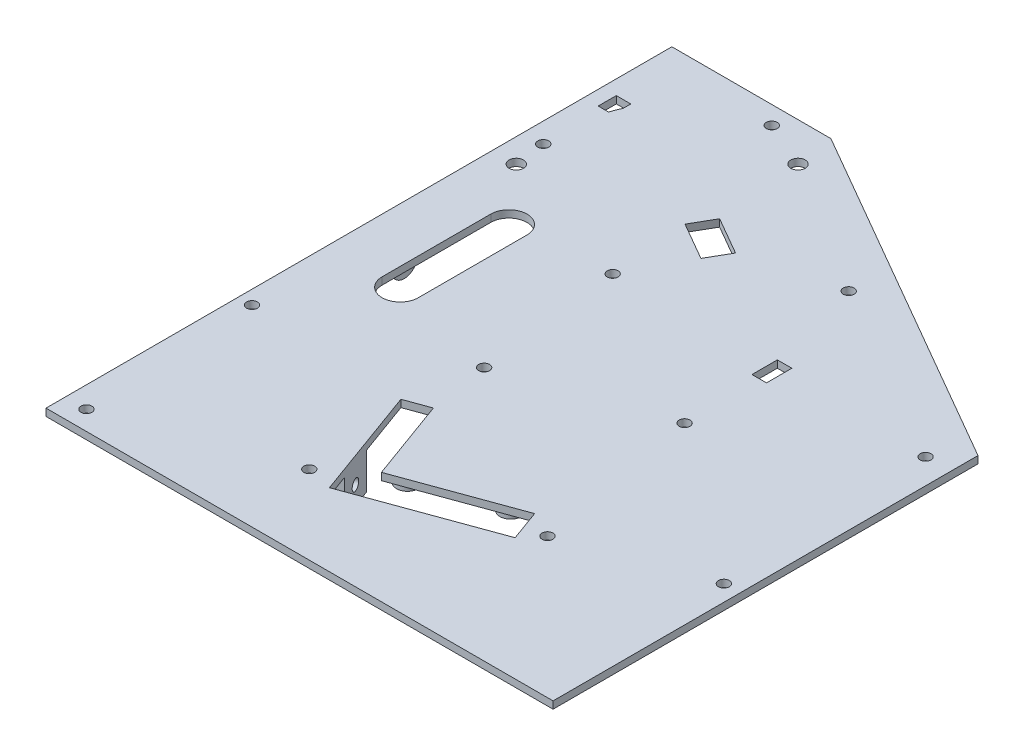
SolidWorks part; units mm, degrees
ref_plane "Front Plane" through (0, 0, 0) normal (0, 0, 1) x (1, 0, 0)
ref_plane "Top Plane" through (0, 0, 0) normal (0, 1, 0) x (1, 0, 0)
ref_plane "Right Plane" through (0, 0, 0) normal (1, 0, 0) x (0, 0, -1)
sketch "Sketch1" plane through (0, 0, 0) normal (0, 1, 0) x (1, 0, 0)
  line L1 (-70, 100) -> (70, 100)
  line L2 (-70, 100) -> (-70, -100)
  line L3 (-70, -100) -> (70, -100)
  line L4 (70, 100) -> (70, -100)
  line L5 (-70, 100) -> (70, -100) construction
  line L6 (-70, -100) -> (70, 100) construction
  point P0 (0, 0)
  dimension "D1" = 200
  dimension "D2" = 140
extrude "Boss-Extrude1" add sketch "Sketch1" along normal blind 2
sketch "Sketch2" plane through (0, 2, 0) normal (0, 1, 0) x (1, 0, 0)
  line L0 (-60, 63) -> (30, 11.0385) construction
  line L1 (-70, 100) -> (-70, -100) construction
  line L2 (70, -14.4027) -> (23.0154, -31.5037) construction
  line L3 (70, -100) -> (70, 100) construction
  line L4 (-50.6218, 98) -> (-70, 98) construction
  line L5 (-60, 63) -> (-50.6218, 63) construction
  line L6 (70, 100) -> (-70, 100) construction
  line L7 (70, -14.4027) -> (47.7176, -14.4027) construction
  line L8 (-51.25, 78.1554) -> (38.75, 26.1939) construction
  line L9 (-60, 63) -> (-70, 63) construction
  line L10 (-50.6218, 98) -> (70, 28.359) construction
  line L11 (-25.7823, 59.4102) -> (-22.2823, 65.4724)
  line L12 (-25.7823, 59.4102) -> (-15.39, 53.4102)
  line L13 (-22.2823, 65.4724) -> (-11.89, 59.4724)
  line L14 (-15.39, 53.4102) -> (-11.89, 59.4724)
  line L15 (-25.7823, 59.4102) -> (-11.89, 59.4724)
  line L16 (-51.25, 78.1554) -> (-70, 78.1554) construction
  line L17 (-50.6218, 98) -> (47.5, 41.3494) construction
  line L18 (-66, 80.6554) -> (-62, 80.6554)
  line L19 (-66, 80.6554) -> (-66, 75.6554)
  line L20 (-66, 75.6554) -> (-62, 75.6554)
  line L21 (-62, 80.6554) -> (-62, 75.6554)
  line L22 (-66, 80.6554) -> (-62, 75.6554) construction
  line L23 (-66, 75.6554) -> (-62, 80.6554) construction
  line L24 (19.4272, 32.69) -> (23.4317, 32.69)
  line L25 (19.4272, 32.69) -> (19.4272, 39.6978)
  line L26 (19.4272, 39.6978) -> (23.4317, 39.6978)
  line L27 (23.4317, 32.69) -> (23.4317, 39.6978)
  line L28 (19.4272, 32.69) -> (23.4317, 39.6978) construction
  line L29 (19.4272, 39.6978) -> (23.4317, 32.69) construction
  line L30 (30, 11.0385) -> (30, -28.9615) construction
  line L31 (-70, -65.3585) -> (-14.5723, -45.1845) construction
  line L32 (30, 11.0385) -> (-70, -25.3585) construction
  circle A0 centre (-43.9688, 69.9102) radius 20
  point P10 (-18.8361, 59.4413)
  point P13 (-64, 78.1554)
  point P25 (-64, 75.6554)
  point P26 (21.4295, 36.1939)
  dimension "D6" = 40
  dimension "D1" = 37
  dimension "D2" = 30
  dimension "D3" = 20
  dimension "D4" = 40
  dimension "D5" = 10
  dimension "D9" = 11
  dimension "D10" = 5
  dimension "D11" = 4
  dimension "D12" = 4
  dimension "D13" = 12
  dimension "D14" = 7
  dimension "D15" = 20
  dimension "D16" = 40
  dimension "D17" = 50
  dimension "D18" = 40
  dimension "D19" = 21
  dimension "D20" = 3.5
  dimension "D7" = 35
  dimension "D8" = 17.5
sketch "Sketch3" plane through (0, 2, 0) normal (0, 1, 0) x (1, 0, 0)
  line L0 (-50.6218, 98) -> (70, 28.359) construction
  line L1 (-60, 63) -> (30, 11.0385) construction
  line L2 (30, 11.0385) -> (-70, -25.3585) construction
  line L3 (70, -14.4027) -> (23.0154, -31.5037) construction
  line L4 (-70, -65.3585) -> (-14.5723, -45.1845) construction
  line L5 (-50.6218, 98) -> (70, 28.359)
  line L6 (-60, 63) -> (30, 11.0385)
  line L7 (30, 11.0385) -> (-70, -25.3585)
  line L8 (70, -14.4027) -> (23.0154, -31.5037)
  line L9 (-70, -65.3585) -> (-14.5723, -45.1845)
  line L10 (-60, 63) -> (-70, 63) construction
  line L11 (-60, 63) -> (-70, 63)
extrude "Cut-Extrude-Thin1" [suppressed] cut sketch "Sketch3" against normal blind 0.5 thin contours L11 L6 L7
sketch "Sketch4" plane through (0, 0, 0) normal (0, -1, 0) x (1, 0, 0)
  circle A0 centre (-43.9688, -69.9102) radius 20 construction
  circle A1 centre (-43.9688, -69.9102) radius 20
extrude "Cut-Extrude1" cut sketch "Sketch4" against normal blind 1
sketch "Sketch6" plane through (0, 0, 0) normal (0, -1, 0) x (1, 0, 0)
  line L0 (-24.5234, -89.3556) -> (-63.4142, -50.4648) construction
  line L1 (-25.9376, -90.7698) -> (-64.8285, -51.879) construction
  line L2 (-23.1092, -87.9414) -> (-62, -49.0505) construction
  line L4 (-51.25, -78.1554) -> (38.75, -26.1939) construction
  arc A0 (-25.9376, -90.7698) -> (-23.1092, -87.9414) centre (-24.5234, -89.3556) ccw construction
  arc A1 (-62, -49.0505) -> (-64.8285, -51.879) centre (-63.4142, -50.4648) ccw construction
  circle A2 centre (-63.4142, -50.4648) radius 2
  circle A3 centre (-24.5234, -89.3556) radius 2
  point P2 (-43.9688, -69.9102)
  dimension "D1" = 55
  dimension "D2" = 4
  dimension "D3" = 105
extrude "Cut-Extrude2" cut sketch "Sketch6" against normal up to next
extrude "Cut-Extrude4" cut sketch "Sketch2" against normal through all and the other way through all contours L15 L12 L14 | L11 L15 L13 | L21 L18 L19 L20 | L24 L27 L26 L25
sketch "Sketch7" plane through (0, 2, 0) normal (0, 1, 0) x (1, 0, 0)
  line L0 (-14.5723, -45.1845) -> (23.0154, -31.5037)
  line L1 (23.0154, -31.5037) -> (25.7515, -39.0213)
  line L2 (25.7515, -39.0213) -> (-11.8362, -52.7021)
  line L3 (-11.8362, -52.7021) -> (-14.5723, -45.1845)
  line L4 (-14.5723, -45.1845) -> (23.0154, -31.5037)
  line L5 (-14.5723, -45.1845) -> (-14.9144, -44.2448)
  line L6 (23.0154, -31.5037) -> (22.6733, -30.564)
  line L7 (-14.9144, -44.2448) -> (22.6733, -30.564)
  line L8 (70, -14.4027) -> (23.0154, -31.5037) construction
  dimension "D1" = 8
  dimension "D2" = 40
  dimension "D3" = 1
extrude "Cut-Extrude5" cut sketch "Sketch7" against normal up to surface (2 mm away) contours L3 L2 L1 L0 | L7 L5 L0 L6 up to face at (21.4295, 0, -36.1939)
sketch "Sketch8" plane through (10.198, 0, -3.7118) normal (-0.9397, 0, 0.342) x (0.342, 0, 0.9397)
  line L1 (38.4755, 0) -> (28.4755, 0)
  line L2 (38.4755, 0) -> (38.4755, -10)
  line L3 (38.4755, -10) -> (28.4755, -10)
  line L4 (28.4755, 0) -> (28.4755, -10)
  line L5 (117.9107, 0) -> (-70.0279, 0) construction
  circle A0 centre (33.4755, -5) radius 1.5
  point P9 (28.4755, -5)
  point P11 (33.4755, -10)
  dimension "D3" = 3
  dimension "D1" = 10
  dimension "D2" = 10
  dimension "D4" = 2
extrude "Boss-Extrude2" add sketch "Sketch8" against normal blind 4
ref_plane "Plane1" through (-8.5959, 0, 3.1286) normal (-0.9397, 0, 0.342) x (0.342, 0, 0.9397)
mirror "Mirror1" about plane through (-8.5959, 0, 3.1286) normal (-0.9397, 0, 0.342) of "Boss-Extrude2"
sketch "Sketch9" plane through (0, 0, 0) normal (0, -1, 0) x (-1, 0, 0)
  line L5 (15.4671, -16.7774) -> (9.3107, -33.6919) construction
  line L6 (16.4068, -17.1194) -> (10.2504, -34.0339)
  line L7 (14.5274, -16.4354) -> (8.3711, -33.3498)
  line L8 (-22.6733, -30.564) -> (14.9144, -44.2448) construction
  line L9 (17.6505, -36.7273) -> (14.2303, -46.1242) construction
  line L10 (18.2862, -17.8035) -> (12.1298, -34.7179)
  line L11 (12.648, -15.7513) -> (6.4917, -32.6658)
  arc A0 (16.4068, -17.1194) -> (14.5274, -16.4354) centre (15.4671, -16.7774) ccw
  arc A1 (8.3711, -33.3498) -> (10.2504, -34.0339) centre (9.3107, -33.6919) ccw
  arc A2 (6.4917, -32.6658) -> (12.1298, -34.7179) centre (9.3107, -33.6919) ccw
  arc A3 (18.2862, -17.8035) -> (12.648, -15.7513) centre (15.4671, -16.7774) ccw
  point P7 (12.3889, -25.2346)
  dimension "D5" = 1
  dimension "D1" = 8
  dimension "D2" = 7.875
  dimension "D3" = 2
  dimension "D7" = 18
extrude "Boss-Extrude4" add sketch "Sketch9" along normal blind 5
mirror "Mirror2" about plane through (-8.5959, 0, 3.1286) normal (-0.9397, 0, 0.342) of "Boss-Extrude4"
sketch "Sketch10" plane through (0, 0, 0) normal (0, -1, 0) x (1, 0, 0)
  line L0 (-28.4653, -55.7631) -> (-19.805, -50.7631)
  line L1 (-28.4653, -55.7631) -> (-32.4653, -48.8349)
  line L2 (-19.805, -50.7631) -> (-23.805, -43.8349)
  line L3 (-32.4653, -48.8349) -> (-23.805, -43.8349)
  line L4 (-25.7823, -59.4102) -> (-15.39, -53.4102) construction
  line L6 (-25.7823, -59.4102) -> (-22.2823, -65.4724) construction
  dimension "D1" = 4.5
  dimension "D2" = 8
  dimension "D3" = 10
  dimension "D4" = 0.5
extrude "Boss-Extrude5" add sketch "Sketch10" along normal blind 23
sketch "Sketch11" plane through (-45.4951, 0, -26.2666) normal (-0.866, 0, -0.5) x (-0.5, 0, 0.866)
  line L0 (-29.0596, -20.0043) -> (-29.0596, -16.0043) construction
  line L1 (-30.0596, -20.0043) -> (-30.0596, -16.0043)
  line L2 (-28.0596, -20.0043) -> (-28.0596, -16.0043)
  line L3 (-26.0596, -23) -> (-34.0596, -23) construction
  line L4 (-26.0596, -23) -> (-26.0596, 0) construction
  line L5 (-29.0596, -6.5043) -> (-29.0596, -2.5043) construction
  line L6 (-30.0596, -6.5043) -> (-30.0596, -2.5043)
  line L7 (-28.0596, -6.5043) -> (-28.0596, -2.5043)
  arc A0 (-30.0596, -20.0043) -> (-28.0596, -20.0043) centre (-29.0596, -20.0043) ccw
  arc A1 (-28.0596, -16.0043) -> (-30.0596, -16.0043) centre (-29.0596, -16.0043) ccw
  arc A2 (-30.0596, -6.5043) -> (-28.0596, -6.5043) centre (-29.0596, -6.5043) ccw
  arc A3 (-28.0596, -2.5043) -> (-30.0596, -2.5043) centre (-29.0596, -2.5043) ccw
  point P3 (-29.0596, -18.0043)
  point P19 (-29.0596, -4.5043)
  dimension "D1" = 2.9957
  dimension "D2" = 4
  dimension "D3" = 3
  dimension "D4" = 2
  dimension "D5" = 13.5
extrude "Cut-Extrude6" cut sketch "Sketch11" against normal up to next (10 mm away)
ref_plane "Plane2" through (21.0298, 0, -36.4247) normal (-0.5, 0, 0.866) x (0.866, 0, 0.5)
mirror "Mirror3" about plane through (21.0298, 0, -36.4247) normal (-0.5, 0, 0.866) of "Cut-Extrude6", "Boss-Extrude5"
hole_wizard "Ø3.0mm Clearance Dowel Hole1" positions "Sketch14" profile "Sketch15" hole size "Ø3.0" standard "ANSI Metric" end condition through all
sketch "Sketch14" plane through (-89.742, 2, 119.4997) normal (0, 1, 0) x (1, 0, 0)
  point P0 (23.5423, 99.781)
  point P1 (25.5944, 52.0145)
  point P2 (70.6996, 68.4315)
  point P3 (70.5269, 116.8821)
  point P4 (111.4918, 131.26)
  point P5 (119.5864, 85.3143)
  point P6 (155.2948, 98.311)
  point P7 (152.8064, 156.4818)
  point P8 (65.8782, 157.0177)
  point P9 (102.577, 185.4818)
  point P10 (52.3475, 214.4818)
  point P11 (25.242, 178.4997)
sketch "Sketch15" plane through (-66.1998, 2, 19.7187) normal (1, 0, 0) x (0, 0, 1)
  line L0 (0, 0) -> (0, 25)
  line L1 (0, 25) -> (1.5, 25)
  line L2 (1.5, 25) -> (1.5, 0)
  line L3 (1.5, 0) -> (0, 0)
  line L4 (0, -6.35) -> (0, 107.95) construction
  dimension "Thru Hole Dia." = 3
  dimension "Thru Hole Depth" = 25
sketch "Sketch16" plane through (0, 2, 0) normal (0, 1, 0) x (1, 0, 0)
  line L1 (-43.6218, 110.1244) -> (83.0261, 110.1244)
  line L2 (-43.6218, 110.1244) -> (77, 40.4833)
  line L3 (-43.6218, 110.1244) -> (77, 40.4833)
  line L4 (83.0261, 110.1244) -> (83.0261, 36.9032)
  line L5 (83.0261, 36.9032) -> (77, 40.4833)
  dimension "D1" = 14
extrude "Cut-Extrude7" cut sketch "Sketch16" against normal through all
sketch "Sketch17" plane through (0, 2, 0) normal (0, 1, 0) x (1, 0, 0)
  line L0 (-43.2303, 98) -> (-26.6218, 98)
  line L1 (-26.6218, 98) -> (68, 43.3701)
  line L2 (68, 43.3701) -> (68, 33.0364)
  line L3 (70, -100) -> (70, 44.5248) construction
  line L4 (-26.0859, 100) -> (70, 44.5248) construction
  line L5 (-26.0859, 100) -> (-70, 100) construction
  line L6 (-43.2303, 98) -> (-46.6944, 100)
  line L7 (-46.6944, 100) -> (-26.0859, 100)
  line L8 (-26.0859, 100) -> (70, 44.5248)
  line L9 (70, 44.5248) -> (70, 31.875)
  line L10 (70, 31.875) -> (68, 33.0364)
  dimension "D1" = 2
  dimension "D2" = 2
  dimension "D3" = 2
extrude "Boss-Extrude6" [suppressed] add sketch "Sketch17" along normal blind 4
sketch "Sketch18" plane through (0, 2, 0) normal (0, 1, 0) x (1, 0, 0)
  line L0 (-70, 100) -> (-70, -100) construction
  line L1 (-70, -72.7995) -> (70, -72.7995)
  line L2 (-70, -72.7995) -> (-70, -100)
  line L3 (-70, -100) -> (70, -100)
  line L4 (70, -72.7995) -> (70, -100)
extrude "Cut-Extrude8" cut sketch "Sketch18" against normal through all
extrude "Cut-Extrude9" cut sketch "Sketch19" against normal through all
sketch "Sketch19" plane through (-89.742, 8, 119.4997) normal (0, 1, 0) x (1, 0, 0)
  line L0 (39.742, 154.4997) -> (39.742, 124.4997) construction
  line L1 (44.742, 154.4997) -> (44.742, 124.4997)
  line L2 (34.742, 154.4997) -> (34.742, 124.4997)
  arc A0 (44.742, 154.4997) -> (34.742, 154.4997) centre (39.742, 154.4997) ccw
  arc A1 (34.742, 124.4997) -> (44.742, 124.4997) centre (39.742, 124.4997) ccw
  point P2 (39.742, 139.4997)
sketch "Sketch20" plane through (-70, 0, 0) normal (-1, 0, 0) x (0, 0, 1)
  line L0 (67.8585, -0.5) -> (67.8585, 8.5) construction
  line L3 (-100, 0) -> (72.7995, 0) construction
  line L4 (55.3585, -3) -> (55.3585, 0)
  line L5 (62.3585, -3) -> (62.3585, 0)
  line L7 (55.3585, 0) -> (62.3585, 0)
  arc A0 (55.3585, -3) -> (62.3585, -3) centre (58.8585, -3) ccw
  circle A1 centre (58.8585, -3) radius 1.5
  dimension "D1" = 2
  dimension "D2" = 3
  dimension "D3" = 3
  dimension "D4" = 5.5
extrude "Boss-Extrude7" add sketch "Sketch20" against normal blind 10
pattern_linear "LPattern1" count 3 spacing 75 along (0, 0, -1) of "Boss-Extrude7"
sketch "Sketch22" plane through (0, 2, 0) normal (0, 1, 0) x (1, 0, 0)
  line L0 (-14.9144, -44.2448) -> (-8.3365, -41.8507)
  line L1 (-14.9144, -44.2448) -> (-23.1228, -21.6922)
  line L2 (-8.3365, -41.8507) -> (-16.545, -19.2981)
  line L3 (-23.1228, -21.6922) -> (-16.545, -19.2981)
  line L4 (-14.9144, -44.2448) -> (22.6733, -30.564) construction
  dimension "D1" = 7
  dimension "D2" = 24
extrude "Cut-Extrude10" cut sketch "Sketch22" against normal up to surface (2 mm away) up to face at (-50, 0, -20)
